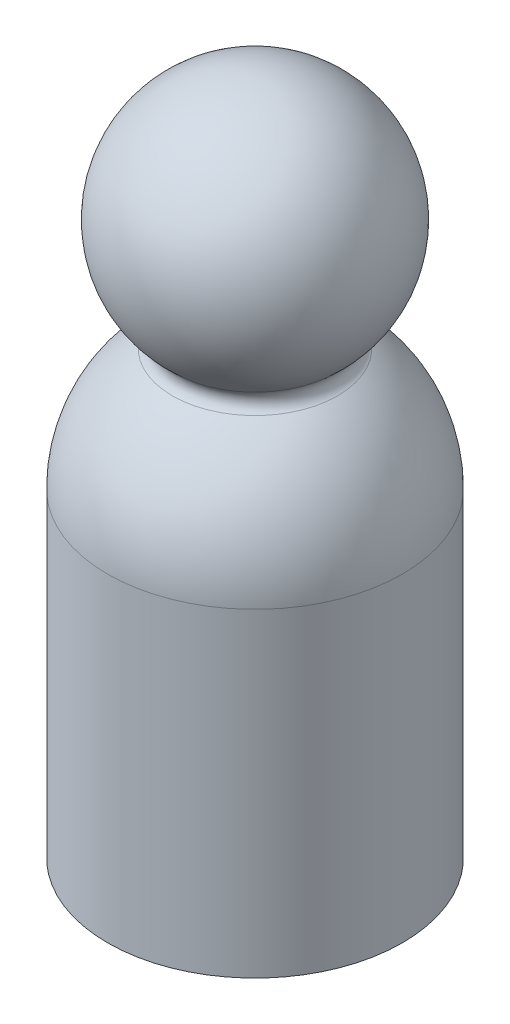
SolidWorks part; units mm, degrees
ref_plane "前基準面" through (0, 0, 0) normal (0, 0, 1) x (1, 0, 0)
ref_plane "上基準面" through (0, 0, 0) normal (0, 1, 0) x (1, 0, 0)
ref_plane "右基準面" through (0, 0, 0) normal (1, 0, 0) x (0, 0, -1)
sketch "草圖1" plane through (0, 0, 0) normal (0, 0, 1) x (1, 0, 0)
  line L0 (0, -20.6899) -> (0, 22.4255) construction
  line L1 (0, 24.5697) -> (0, -30.4303)
  line L3 (-12, -4.4303) -> (-12, -30.4303)
  line L4 (-12, -30.4303) -> (0, -30.4303)
  arc A0 (0, 24.5697) -> (-5.5145, 6.2276) centre (0, 14.5697) ccw
  arc A1 (-5.5145, 6.2276) -> (-12, -4.4303) centre (0, -4.4303) ccw
  dimension "D2" = 20
  dimension "D3" = 24
  dimension "D1" = 19
revolve "旋轉1" add sketch "草圖1" angle 360 about L0
fillet "圓角1" radius 1 1 edges at (0, 6.2276, -5.5145)
